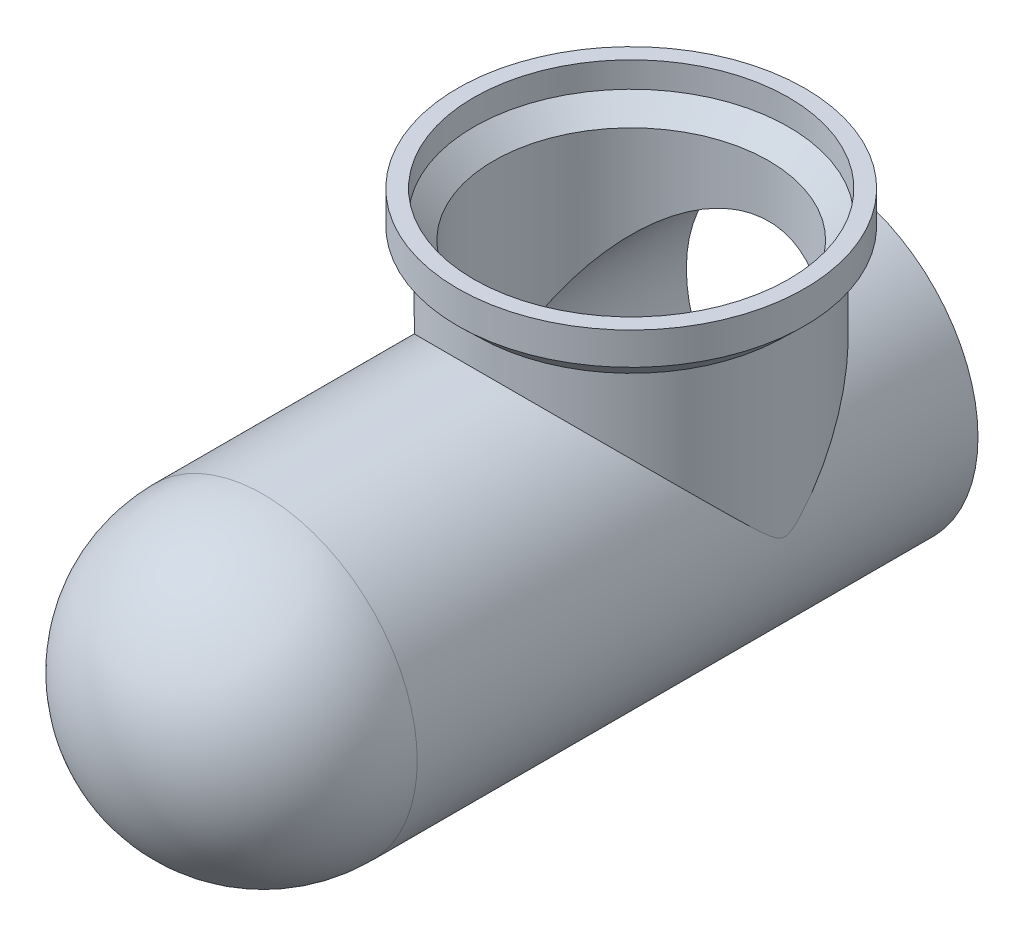
SolidWorks part; units mm, degrees
material "2014-T4"
ref_plane "Front Plane" through (0, 0, 0) normal (0, 0, 1) x (1, 0, 0)
ref_plane "Top Plane" through (0, 0, 0) normal (0, 1, 0) x (1, 0, 0)
ref_plane "Right Plane" through (0, 0, 0) normal (1, 0, 0) x (0, 0, -1)
sketch "Sketch1" plane through (0, 0, 0) normal (0, 0, 1) x (1, 0, 0)
  circle A0 centre (0, 0) radius 47.85
  dimension "D1" = 95.7
extrude "Boss-Extrude1" add sketch "Sketch1" along normal blind 222.25
ref_plane "Plane1" through (0, 57, 0) normal (0, 1, 0) x (1, 0, 0)
sketch "Sketch2" plane through (0, 57, 0) normal (0, 1, 0) x (1, 0, 0)
  circle A0 centre (0, -60) radius 47.75
  point P0 (0, 0)
  dimension "D1" = 95.5
  dimension "D2" = 60
extrude "Boss-Extrude2" add sketch "Sketch2" against normal blind 57
sketch "Sketch5" plane through (0, 0, 0) normal (1, 0, 0) x (0, 0, -1)
  line L0 (-12.25, 57) -> (-107.75, 57) construction
  line L1 (-12.25, 57) -> (-107.75, 57)
  line L2 (-12.25, 57) -> (-6.025, 63)
  line L3 (-6.025, 63) -> (-6.025, 73.05)
  line L4 (-6.025, 73.05) -> (-60, 73.05)
  line L5 (-60, 73.05) -> (-60, 57)
  dimension "D1" = 16.05
  dimension "D2" = 6
  dimension "D3" = 53.975
revolve "Revolve3" add sketch "Sketch5" angle 360 about L5
fillet "Fillet1" radius 47.85 1 edges at (47.85, 0, 222.25)
shell "Shell1" thickness 5
